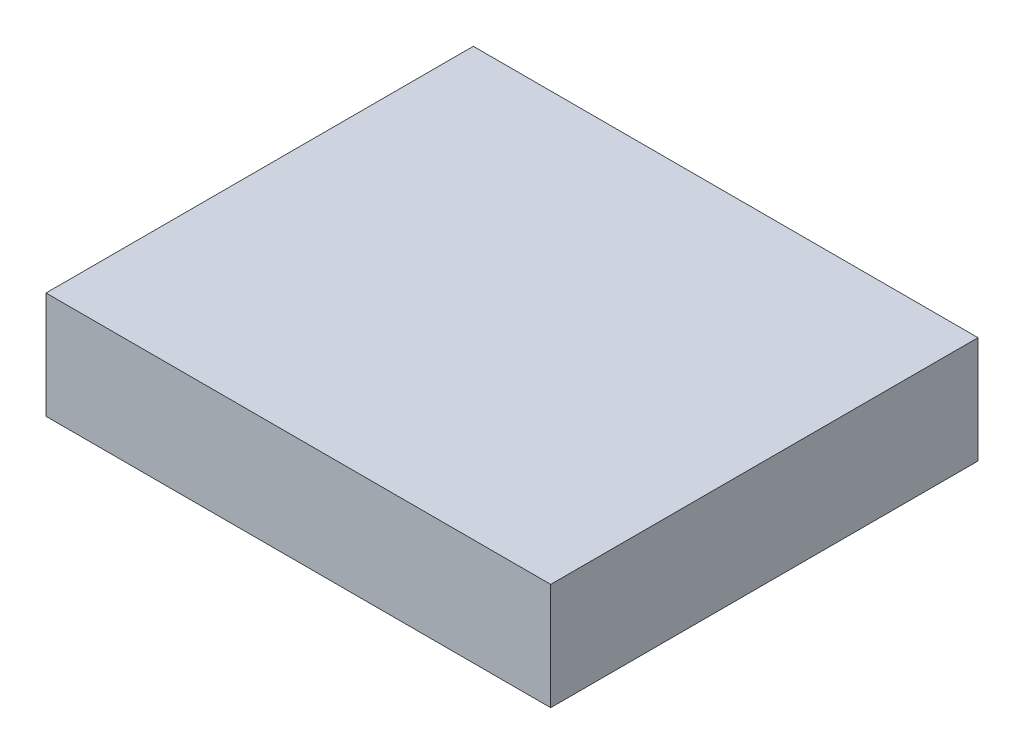
SolidWorks part; units mm, degrees
ref_plane "Front Plane" through (0, 0, 0) normal (0, 0, 1) x (1, 0, 0)
ref_plane "Top Plane" through (0, 0, 0) normal (0, 1, 0) x (1, 0, 0)
ref_plane "Right Plane" through (0, 0, 0) normal (1, 0, 0) x (0, 0, -1)
sketch "Sketch1" plane through (0, 0, 0) normal (0, 1, 0) x (1, 0, 0)
  line L1 (0, 0) -> (30, 0)
  line L2 (0, 0) -> (0, -25.4)
  line L3 (0, -25.4) -> (30, -25.4)
  line L4 (30, 0) -> (30, -25.4)
  dimension "D1" = 30
  dimension "D2" = 25.4
extrude "Boss-Extrude1" add sketch "Sketch1" against normal blind 6.35
